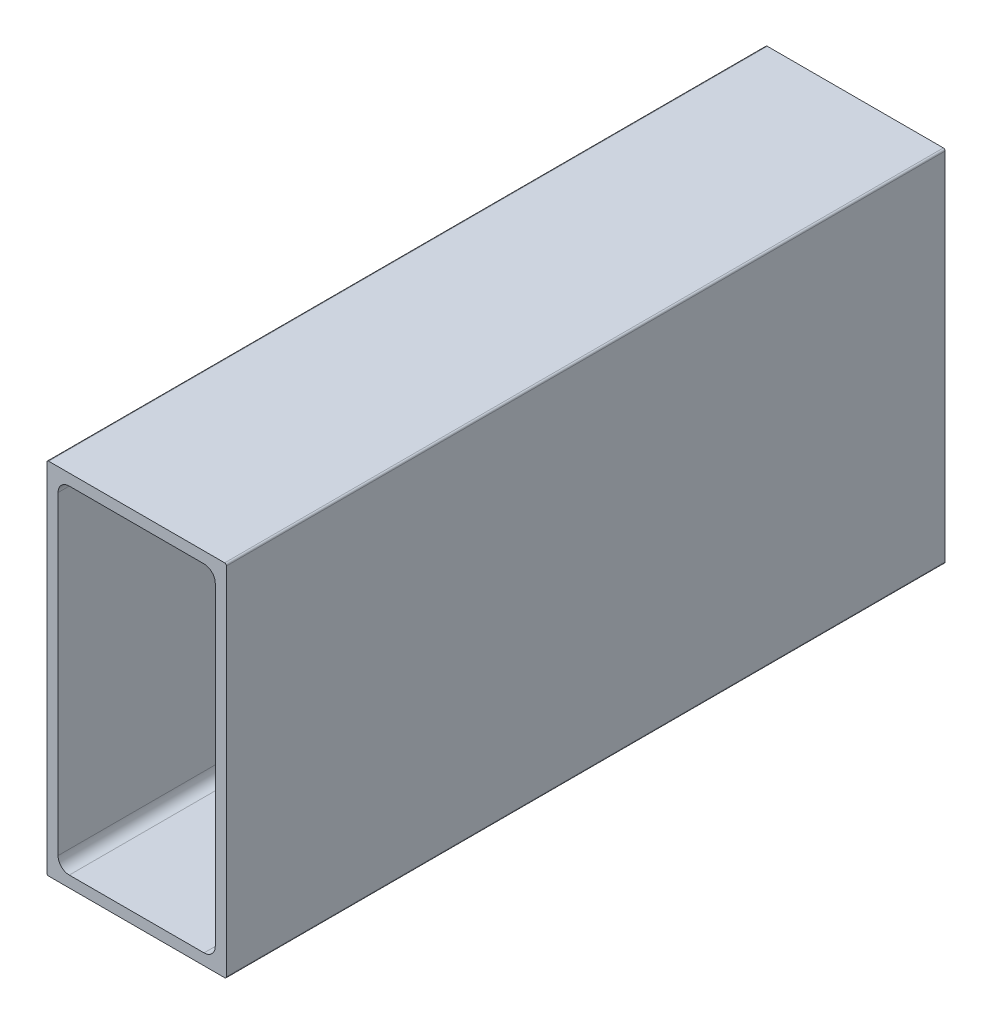
SolidWorks part; units mm, degrees
material "6061 Alloy"
ref_plane "Front Plane" through (0, 0, 0) normal (0, 0, 1) x (1, 0, 0)
ref_plane "Top Plane" through (0, 0, 0) normal (0, 1, 0) x (1, 0, 0)
ref_plane "Right Plane" through (0, 0, 0) normal (1, 0, 0) x (0, 0, -1)
ref_plane "Plane1" through (0, 0, 0) normal (0, 0, -1) x (-1, 0, 0)
sketch "Sketch1" plane through (0, 0, 0) normal (0, 0, -1) x (-1, 0, 0)
  line L0 (-11.1125, -22.225) -> (-11.1125, 22.225)
  line L1 (-9.525, 23.8125) -> (9.525, 23.8125)
  line L2 (11.1125, 22.225) -> (11.1125, -22.225)
  line L3 (9.525, -23.8125) -> (-9.525, -23.8125)
  line L4 (-12.7, 25.146) -> (-12.7, -25.146)
  line L5 (-12.446, -25.4) -> (12.446, -25.4)
  line L6 (12.7, -25.146) -> (12.7, 25.146)
  line L7 (12.446, 25.4) -> (-12.446, 25.4)
  arc A0 (-11.1125, 22.225) -> (-9.525, 23.8125) centre (-9.525, 22.225) cw
  arc A1 (9.525, 23.8125) -> (11.1125, 22.225) centre (9.525, 22.225) cw
  arc A2 (11.1125, -22.225) -> (9.525, -23.8125) centre (9.525, -22.225) cw
  arc A3 (-9.525, -23.8125) -> (-11.1125, -22.225) centre (-9.525, -22.225) cw
  arc A4 (-12.7, -25.146) -> (-12.446, -25.4) centre (-12.446, -25.146) ccw
  arc A5 (12.446, -25.4) -> (12.7, -25.146) centre (12.446, -25.146) ccw
  arc A6 (12.7, 25.146) -> (12.446, 25.4) centre (12.446, 25.146) ccw
  arc A7 (-12.446, 25.4) -> (-12.7, 25.146) centre (-12.446, 25.146) ccw
extrude "Boss-Extrude1" add sketch "Sketch1" against normal blind 101.6
